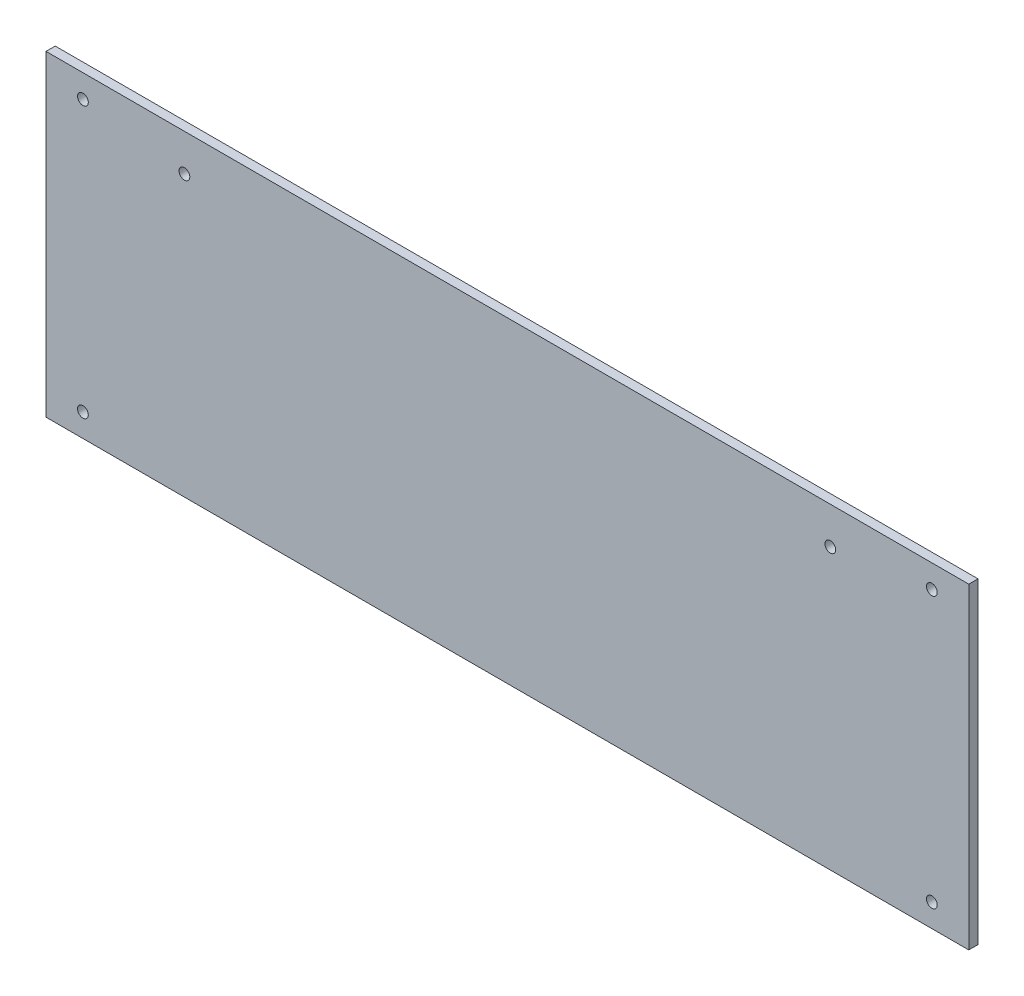
SolidWorks part; units mm, degrees
ref_plane "Front Plane" through (0, 0, 0) normal (0, 0, 1) x (1, 0, 0)
ref_plane "Top Plane" through (0, 0, 0) normal (0, 1, 0) x (1, 0, 0)
ref_plane "Right Plane" through (0, 0, 0) normal (1, 0, 0) x (0, 0, -1)
ref_plane "Plane1" through (0, 0, 3) normal (0, 0, 1) x (1, 0, 0)
sketch "Sketch1" plane through (0, 0, 3) normal (0, 0, 1) x (1, 0, 0)
  line L0 (0, -3) -> (300, -3)
  line L1 (300, -3) -> (300, 100)
  line L2 (300, 100) -> (0, 100)
  line L3 (0, 100) -> (0, -3)
  circle A0 centre (288, 92.5) radius 1.75
  circle A1 centre (12, 92.5) radius 1.75
  circle A2 centre (12, 4.5) radius 1.75
  circle A3 centre (288, 4.5) radius 1.75
  circle A4 centre (45, 88) radius 1.75
  circle A5 centre (255, 88) radius 1.75
extrude "Boss-Extrude1" add sketch "Sketch1" against normal blind 3
